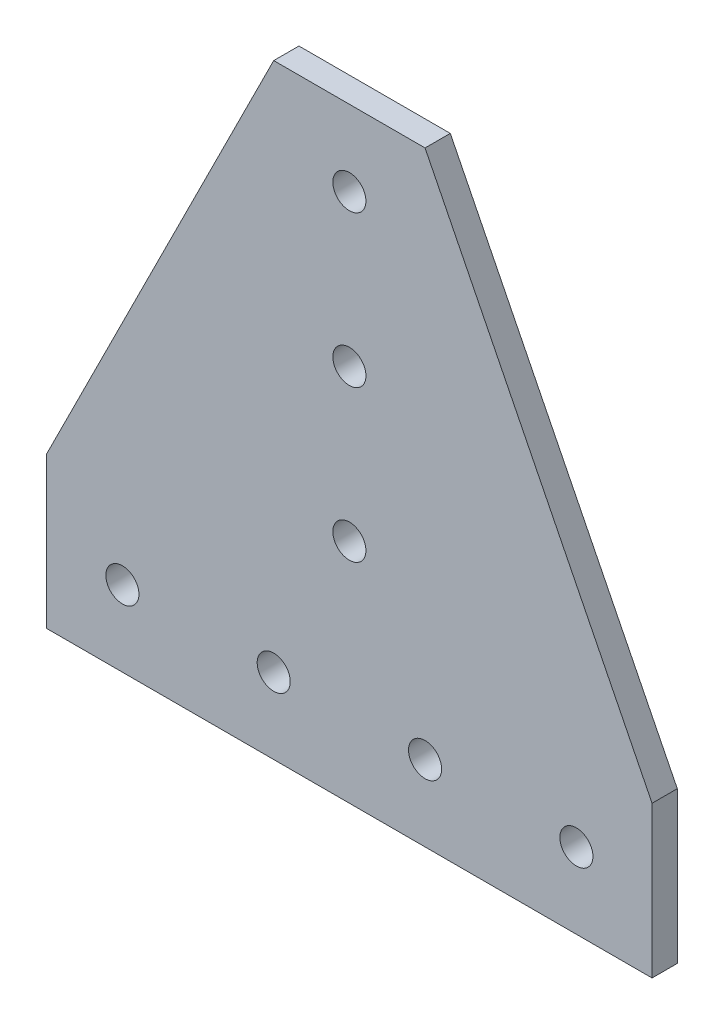
SolidWorks part; units mm, degrees
ref_plane "Front Plane" through (0, 0, 0) normal (0, 0, 1) x (1, 0, 0)
ref_plane "Top Plane" through (0, 0, 0) normal (0, 1, 0) x (1, 0, 0)
ref_plane "Right Plane" through (0, 0, 0) normal (1, 0, 0) x (0, 0, -1)
ref_plane "Plane1" through (0, 0, 6.35) normal (0, 0, 1) x (1, 0, 0)
sketch "Sketch1" plane through (0, 0, 6.35) normal (0, 0, 1) x (1, 0, 0)
  line L0 (-19.05, 152.4) -> (-76.2, 38.1)
  line L1 (-76.2, 38.1) -> (-76.2, 0)
  line L2 (-76.2, 0) -> (76.2, 0)
  line L3 (76.2, 0) -> (76.2, 38.1)
  line L4 (76.2, 38.1) -> (19.05, 152.4)
  line L5 (19.05, 152.4) -> (-19.05, 152.4)
  circle A0 centre (-57.15, 19.05) radius 4.1656
  circle A1 centre (-19.05, 19.05) radius 4.1656
  circle A2 centre (0, 133.35) radius 4.1656
  circle A3 centre (0, 95.25) radius 4.1656
  circle A4 centre (0, 57.15) radius 4.1656
  circle A5 centre (19.05, 19.05) radius 4.1656
  circle A6 centre (57.15, 19.05) radius 4.1656
extrude "Boss-Extrude1" add sketch "Sketch1" against normal blind 6.35
